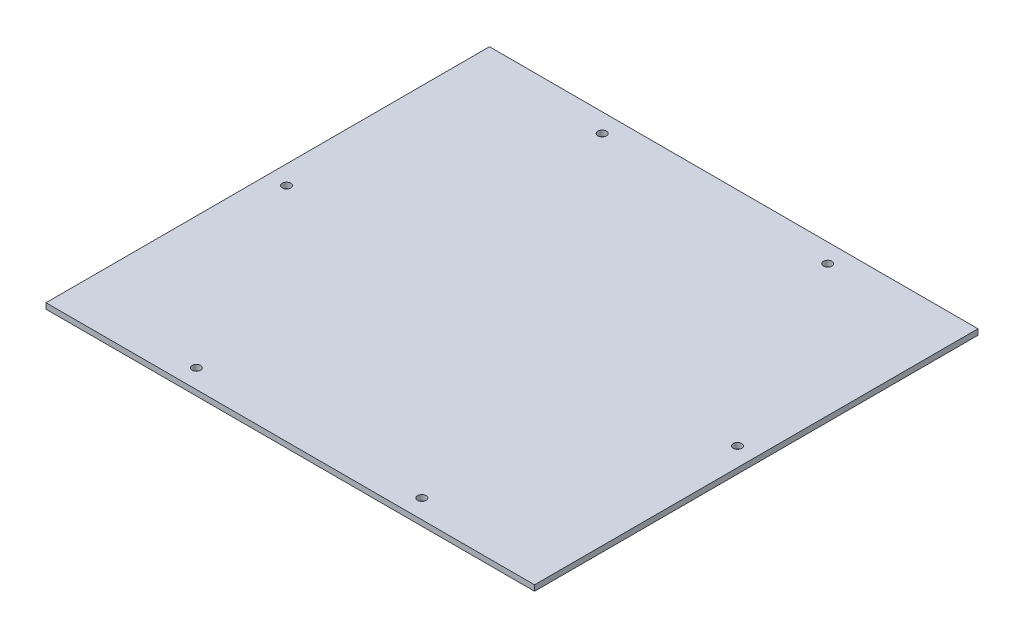
SolidWorks part; units mm, degrees
ref_plane "Спереди" through (0, 0, 0) normal (0, 0, 1) x (1, 0, 0)
ref_plane "Сверху" through (0, 0, 0) normal (0, 1, 0) x (1, 0, 0)
ref_plane "Справа" through (0, 0, 0) normal (1, 0, 0) x (0, 0, -1)
sketch "Эскиз1" plane through (0, 30, 0) normal (0, 1, 0) x (1, 0, 0)
  line L0 (30.4991, -236.0645) -> (34.1691, -236.0645) construction
  line L1 (35.6691, -234.5645) -> (35.6691, -230.8945) construction
  line L2 (30.4991, -236.0645) -> (34.1691, -236.0645) construction
  line L3 (35.6691, -234.5645) -> (35.6691, -230.8945) construction
  line L4 (35.6691, -1.5645) -> (35.6691, -5.2345) construction
  line L5 (30.4991, -0.0645) -> (34.1691, -0.0645) construction
  line L6 (35.6691, -1.5645) -> (35.6691, -5.2345) construction
  line L7 (30.4991, -0.0645) -> (34.1691, -0.0645) construction
  line L8 (-219.1609, -0.0645) -> (-222.8309, -0.0645) construction
  line L9 (-224.3309, -1.5645) -> (-224.3309, -5.2345) construction
  line L10 (-219.1609, -0.0645) -> (-222.8309, -0.0645) construction
  line L11 (-224.3309, -1.5645) -> (-224.3309, -5.2345) construction
  line L12 (-224.3309, -234.5645) -> (-224.3309, -230.8945) construction
  line L13 (-219.1609, -236.0645) -> (-222.8309, -236.0645) construction
  line L14 (-224.3309, -234.5645) -> (-224.3309, -230.8945) construction
  line L15 (-219.1609, -236.0645) -> (-222.8309, -236.0645) construction
  line L16 (-224.3309, -0.0645) -> (35.6691, -0.0645)
  line L17 (-224.3309, -0.0645) -> (-224.3309, -236.0645)
  line L18 (35.6691, -0.0645) -> (35.6691, -236.0645)
  line L19 (-224.3309, -236.0645) -> (35.6691, -236.0645)
  dimension "D1" = 0
  dimension "D2" = 0
extrude "Бобышка-Вытянуть1" add sketch "Эскиз1" along normal blind 3
sketch "Эскиз2" plane through (0, 33, 0) normal (0, 1, 0) x (1, 0, 0)
  line L0 (-214.3309, -10.0645) -> (25.6691, -10.0645) construction
  line L1 (-214.3309, -10.0645) -> (-214.3309, -226.0645) construction
  line L2 (25.6691, -10.0645) -> (25.6691, -226.0645) construction
  line L3 (-214.3309, -226.0645) -> (25.6691, -226.0645) construction
  line L4 (-224.3309, -0.0645) -> (-224.3309, -236.0645) construction
  line L5 (35.6691, -236.0645) -> (35.6691, -0.0645) construction
  line L6 (-224.3309, -236.0645) -> (35.6691, -236.0645) construction
  line L7 (35.6691, -0.0645) -> (-224.3309, -0.0645) construction
  line L8 (-154.3309, -10.0645) -> (-154.3309, -226.0645) construction
  line L9 (-34.3309, -10.0645) -> (-34.3309, -226.0645) construction
  circle A0 centre (-214.3309, -118.0645) radius 2.25
  circle A1 centre (-154.3309, -10.0645) radius 2.25
  circle A2 centre (-34.3309, -10.0645) radius 2.25
  circle A3 centre (-154.3309, -226.0645) radius 2.25
  circle A4 centre (-34.3309, -226.0645) radius 2.25
  circle A5 centre (25.6691, -118.0645) radius 2.25
  dimension "D5" = 70
  dimension "D7" = 4.5
  dimension "D8" = 4.5
  dimension "D9" = 4.5
  dimension "D10" = 4.5
  dimension "D11" = 4.5
  dimension "D12" = 4.5
  dimension "D1" = 10
  dimension "D2" = 10
  dimension "D3" = 10
  dimension "D4" = 10
  dimension "D6" = 70
extrude "Вырез-Вытянуть1" cut sketch "Эскиз2" against normal through all
